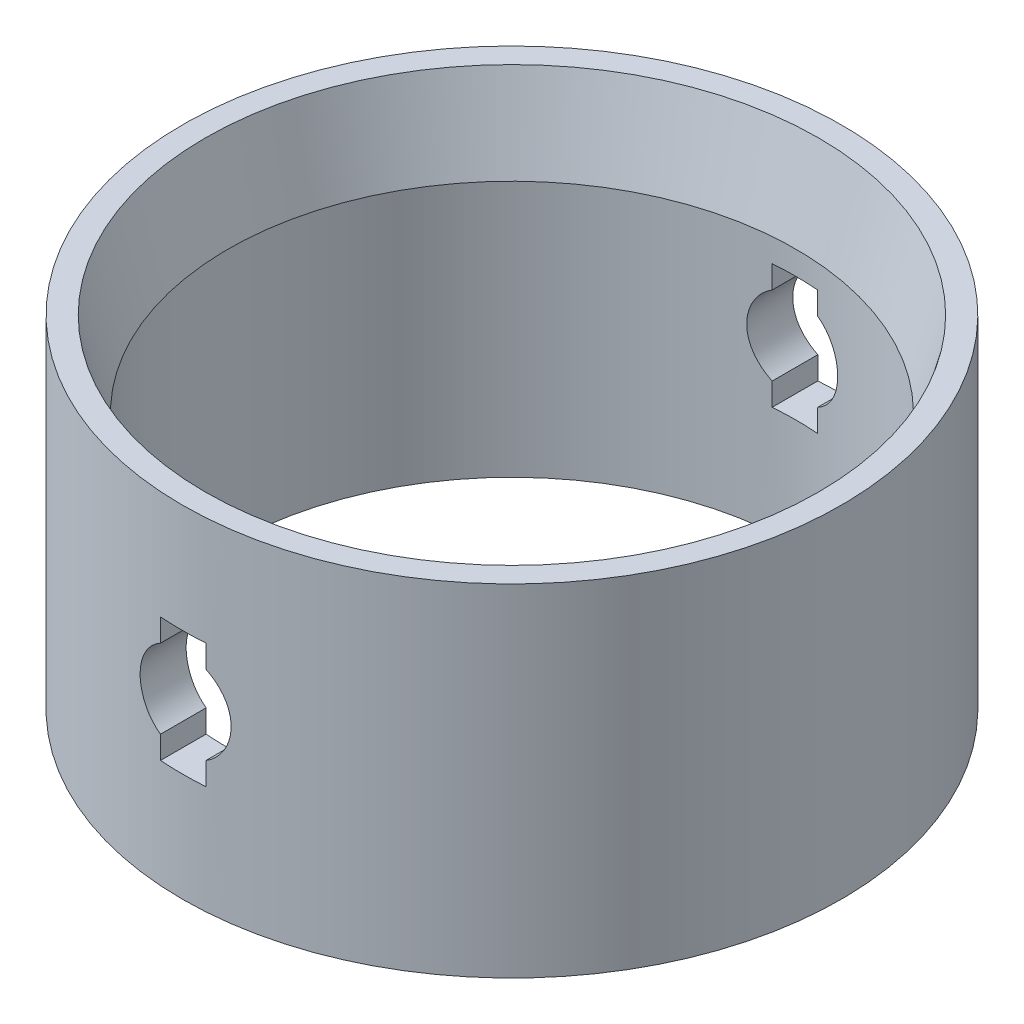
SolidWorks part; units mm, degrees
ref_plane "Front Plane" through (0, 0, 0) normal (0, 0, 1) x (1, 0, 0)
ref_plane "Top Plane" through (0, 0, 0) normal (0, 1, 0) x (1, 0, 0)
ref_plane "Right Plane" through (0, 0, 0) normal (1, 0, 0) x (0, 0, -1)
sketch "Sketch1" plane through (0, 0, 0) normal (0, 1, 0) x (1, 0, 0)
  circle A0 centre (0, 0) radius 62.39
  circle A1 centre (0, 0) radius 72.39
  dimension "D1" = 144.78
  dimension "D2" = 10
extrude "Boss-Extrude1" add sketch "Sketch1" along normal blind 75
sketch "Sketch2" plane through (0, 0, 0) normal (0, 0, 1) x (1, 0, 0)
  line L0 (5, 28.8397) -> (5, 23.8397)
  line L1 (0, 0) -> (0, 75) construction
  line L2 (-72.39, 0) -> (72.39, 0) construction
  line L3 (72.39, 75) -> (-72.39, 75) construction
  line L4 (5, 23.8397) -> (-5, 23.8397)
  line L5 (-5, 23.8397) -> (-5, 28.8397)
  line L6 (-5, 46.1603) -> (-5, 51.1603)
  line L7 (-5, 51.1603) -> (5, 51.1603)
  line L8 (5, 51.1603) -> (5, 46.1603)
  line L9 (0, 23.8397) -> (0, 51.1603) construction
  arc A0 (5, 28.8397) -> (5, 46.1603) centre (0, 37.5) ccw
  arc A1 (-5, 46.1603) -> (-5, 28.8397) centre (0, 37.5) ccw
  point P15 (4.172, 37.5)
  dimension "D2" = 20
  dimension "D1" = 5
  dimension "D3" = 10
extrude "Cut-Extrude1" cut sketch "Sketch2" against normal through all both and the other way through all contours A0 L8 L7 L6 A1 L5 L4 L0
chamfer "Chamfer1" distance 5 angle 75 1 edges at (0, 75, 62.39)
